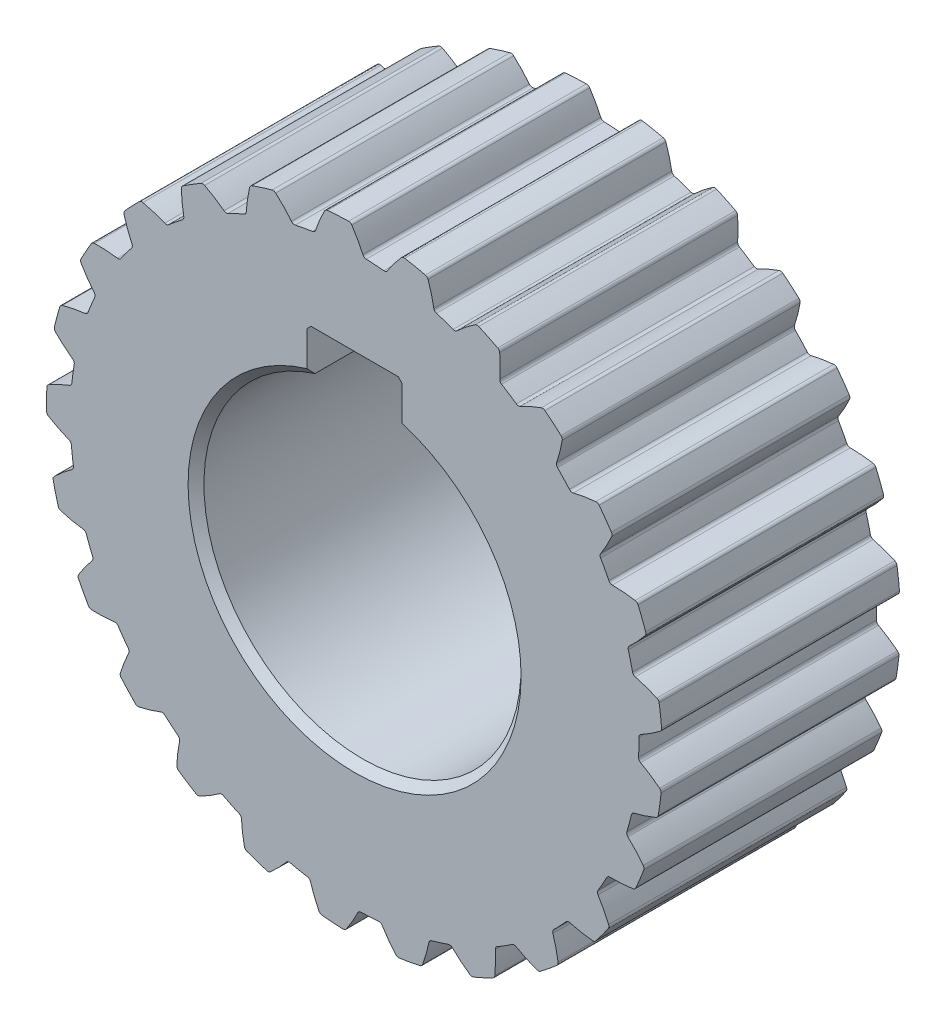
SolidWorks part; units mm, degrees
material "1.6587 (18CrNiMo7-6)"
ref_plane "Front Plane" through (0, 0, 0) normal (0, 0, 1) x (1, 0, 0)
ref_plane "Top Plane" through (0, 0, 0) normal (0, 1, 0) x (1, 0, 0)
ref_plane "Right Plane" through (0, 0, 0) normal (1, 0, 0) x (0, 0, -1)
sketch "Sketch1" plane through (0, 0, 0) normal (0, 0, 1) x (1, 0, 0)
  line L0 (0, 0) -> (0, 25) construction
  line L1 (6, 19.0788) -> (6, 25)
  line L2 (-6, 19.0788) -> (-6, 25)
  line L4 (6, 25) -> (-6, 25)
  line L5 (6, 0) -> (6, 25) construction
  line L6 (-6, 0) -> (-6, 25) construction
  arc A0 (-6, 19.0788) -> (6, 19.0788) centre (0, 0) ccw
  circle A1 centre (0, 0) radius 35.85
  dimension "D1" = 40
  dimension "D2" = 25
  dimension "D5" = 71.7
  dimension "D3" = 6
  dimension "D4" = 6
extrude "Boss-Extrude1" add sketch "Sketch1" along normal blind 30
sketch "Sketch2" plane through (0, 0, 0) normal (0, 0, 1) x (1, 0, 0)
  line L0 (0, 0) -> (37.4458, 2.0146) construction
  line L1 (0, 0) -> (43.1943, 5.0586) construction
  circle A0 centre (0, 0) radius 37.5 construction
  arc A1 (35.8337, 1.0823) -> (35.1141, 7.2266) centre (0, 0) ccw
  arc A2 (38.7391, 2.9334) -> (38.3686, 6.0969) centre (0, 0) ccw
  spline S0 degree 4 poles (32.476, 0) (32.4878, 0.0002) (32.5208, 0.0012) (32.5831, 0.0053) (32.6846, 0.0149) (32.8137, 0.0317) (32.9801, 0.0585) (33.1755, 0.0965) (33.3894, 0.1451) (33.621, 0.2054) (33.8511, 0.2719) (34.0795, 0.3443) (34.306, 0.4218) (34.5791, 0.522) (34.9046, 0.651) (35.282, 0.8145) (35.7061, 1.0148) (36.1339, 1.2349) (36.551, 1.4643) (36.9676, 1.7109) (37.3672, 1.9599) (37.7769, 2.2334) (38.1524, 2.4934) (38.5668, 2.801) (38.8993, 3.0539) (39.3308, 3.4046) (39.5835, 3.6168) (39.8766, 3.8709) (40.0054, 3.9868) (40.0847, 4.0581) knots 0 0 0 0 0 0.005377 0.015084 0.028532 0.04661 0.064855 0.092111 0.119476 0.146842 0.174209 0.201575 0.228941 0.256307 0.307035 0.361767 0.4165 0.471232 0.525964 0.580697 0.635429 0.690161 0.744894 0.799626 0.854358 0.909091 0.954545 1 1 1 1 1 construction
  spline S1 degree 4 poles (35.8337, 1.0823) (35.8551, 1.0931) (35.9835, 1.1583) (36.2172, 1.2807) (36.551, 1.4643) (36.9676, 1.7109) (37.3672, 1.9599) (37.7769, 2.2334) (38.1524, 2.4934) (38.4645, 2.725) (38.6453, 2.8613) (38.738, 2.9325) (38.7391, 2.9334) knots 0.405523 0.405523 0.405523 0.405523 0.405523 0.4165 0.471232 0.525964 0.580697 0.635429 0.690161 0.744894 0.799626 0.800307 0.800307 0.800307 0.800307 0.800307
  spline S2 degree 4 poles (35.1141, 7.2266) (35.1375, 7.221) (35.2774, 7.1873) (35.5331, 7.1222) (35.9002, 7.0206) (36.3625, 6.877) (36.8089, 6.7271) (37.2707, 6.5556) (37.6962, 6.3894) (38.0533, 6.2362) (38.2607, 6.1453) (38.3673, 6.0975) (38.3686, 6.0969) knots 0.405523 0.405523 0.405523 0.405523 0.405523 0.4165 0.471232 0.525964 0.580697 0.635429 0.690161 0.744894 0.799626 0.800307 0.800307 0.800307 0.800307 0.800307
  dimension "D1" = 75
  dimension "D2" = 71.7
  dimension "D3" = 77.7
  dimension "D4" = 3.6
extrude "Boss-Extrude2" add sketch "Sketch2" along normal blind 30
fillet "Fillet1" radius 0.48 4 edges at (35.8337, 1.0823, 15) (38.7391, 2.9334, 15) (38.3686, 6.0969, 15) (35.1141, 7.2266, 15)
pattern_circular "CirPattern1" count 25 over 360 about axis through (0, 0, 30) along (0, 0, -1) of "Boss-Extrude2", "Fillet1"
chamfer "Chamfer1" distance 0.5 2 edges at (6, 25, 15) (-6, 25, 15)
chamfer "Chamfer2" distance 1 2 edges at (0, -20, 0) (0, -20, 30)
